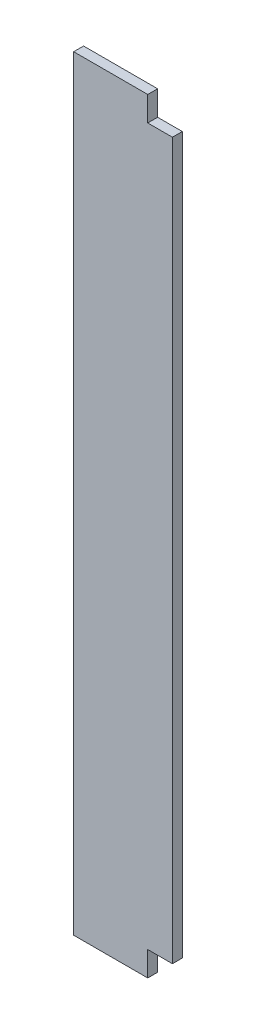
SolidWorks part; units mm, degrees
ref_plane "Plano frontal" through (0, 0, 0) normal (0, 0, 1) x (1, 0, 0)
ref_plane "Plano superior" through (0, 0, 0) normal (0, 1, 0) x (1, 0, 0)
ref_plane "Plano direito" through (0, 0, 0) normal (1, 0, 0) x (0, 0, -1)
sketch "Esboço1" plane through (0, 0, 0) normal (0, 1, 0) x (1, 0, 0)
  line L1 (-129.6089, 67.4581) -> (70.3911, 67.4581)
  line L2 (-129.6089, 67.4581) -> (-129.6089, 47.4581)
  line L3 (-129.6089, 47.4581) -> (70.3911, 47.4581)
  line L4 (70.3911, 67.4581) -> (70.3911, 47.4581)
  dimension "D1" = 200
  dimension "D2" = 20
extrude "Ressalto-extrusão1" add sketch "Esboço1" along normal blind 1550
sketch "Esboço2" plane through (0, 0, -47.4581) normal (0, 0, 1) x (1, 0, 0)
  line L1 (70.3911, 0) -> (20.3911, 0)
  line L2 (70.3911, 0) -> (70.3911, 50)
  line L3 (70.3911, 50) -> (20.3911, 50)
  line L4 (20.3911, 0) -> (20.3911, 50)
  dimension "D1" = 50
  dimension "D2" = 50
extrude "Corte-extrusão1" cut sketch "Esboço2" against normal through all
sketch "Esboço3" plane through (0, 0, -47.4581) normal (0, 0, 1) x (1, 0, 0)
  line L1 (70.3911, 1550) -> (20.3911, 1550)
  line L2 (70.3911, 1550) -> (70.3911, 1500)
  line L3 (70.3911, 1500) -> (20.3911, 1500)
  line L4 (20.3911, 1550) -> (20.3911, 1500)
  dimension "D1" = 50
  dimension "D2" = 50
extrude "Corte-extrusão2" cut sketch "Esboço3" against normal through all
